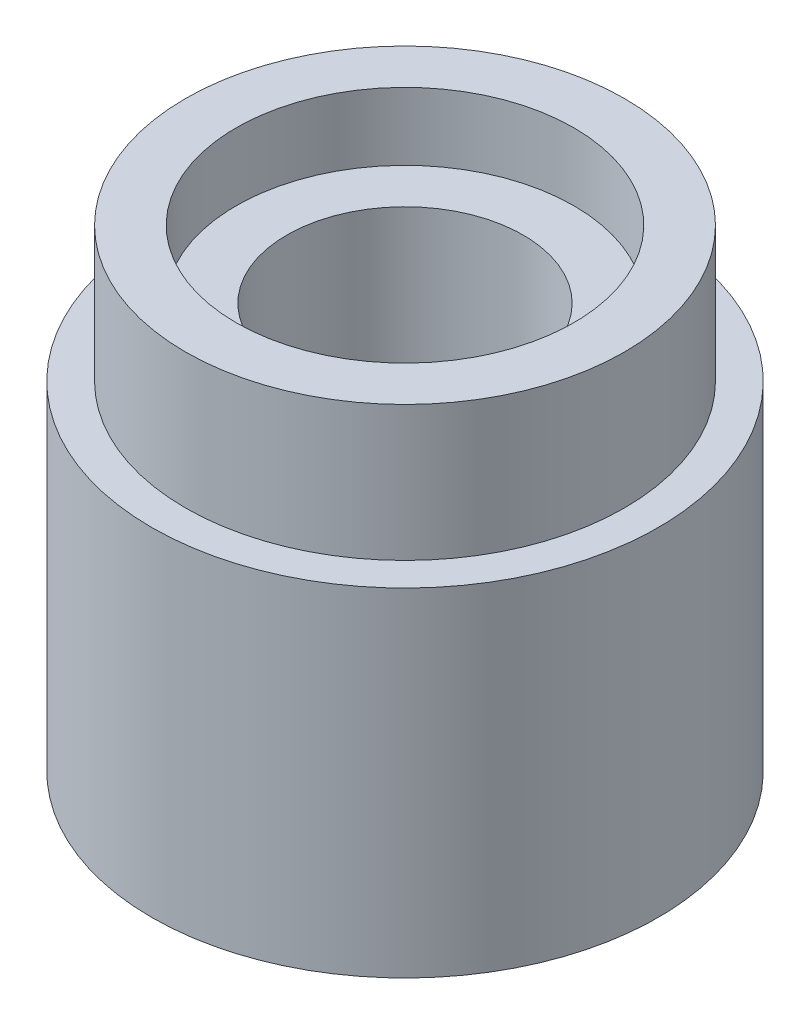
SolidWorks part; units mm, degrees
ref_plane "Front Plane" through (0, 0, 0) normal (0, 0, 1) x (1, 0, 0)
ref_plane "Top Plane" through (0, 0, 0) normal (0, 1, 0) x (1, 0, 0)
ref_plane "Right Plane" through (0, 0, 0) normal (1, 0, 0) x (0, 0, -1)
sketch "Sketch1" plane through (0, 0, 0) normal (0, 1, 0) x (1, 0, 0)
  circle A0 centre (0, 0) radius 3.75
extrude "Boss-Extrude1" add sketch "Sketch1" along normal blind 7
sketch "Sketch2" plane through (0, 7, 0) normal (0, 1, 0) x (1, 0, 0)
  circle A0 centre (0, 0) radius 2.5
  circle A1 centre (0, 0) radius 3.75
sketch "Sketch3" plane through (0, 7, 0) normal (0, 1, 0) x (1, 0, 0)
  circle A0 centre (0, 0) radius 3.25
  circle A1 centre (0, 0) radius 3.75
extrude "Cut-Extrude1" cut sketch "Sketch3" against normal blind 2
sketch "Sketch4" plane through (0, 7, 0) normal (0, 1, 0) x (1, 0, 0)
  circle A0 centre (0, 0) radius 1.75
extrude "Cut-Extrude2" cut sketch "Sketch4" against normal blind 6.5
sketch "Sketch5" plane through (0, 7, 0) normal (0, 1, 0) x (1, 0, 0)
  circle A0 centre (0, 0) radius 2.5
extrude "Cut-Extrude4" cut sketch "Sketch5" against normal blind 1
